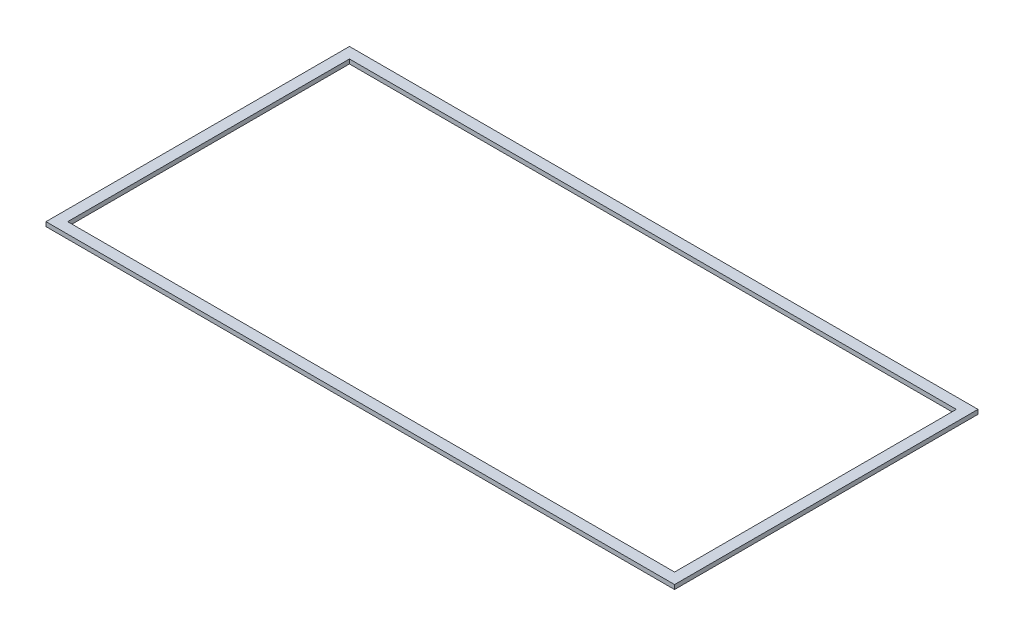
SolidWorks part; units mm, degrees
material "Rubber"
ref_plane "Front Plane" through (0, 0, 0) normal (0, 0, 1) x (1, 0, 0)
ref_plane "Top Plane" through (0, 0, 0) normal (0, 1, 0) x (1, 0, 0)
ref_plane "Right Plane" through (0, 0, 0) normal (1, 0, 0) x (0, 0, -1)
sketch "Sketch1" plane through (0, 0, 0) normal (0, 1, 0) x (1, 0, 0)
  line L1 (-140, -65) -> (140, -65)
  line L2 (-140, -65) -> (-140, 65)
  line L3 (-140, 65) -> (140, 65)
  line L4 (140, -65) -> (140, 65)
  line L5 (-140, -65) -> (140, 65) construction
  line L6 (-140, 65) -> (140, -65) construction
  line L7 (-145, -70) -> (145, -70)
  line L8 (-145, -70) -> (-145, 70)
  line L9 (-145, 70) -> (145, 70)
  line L10 (145, -70) -> (145, 70)
  line L11 (-145, -70) -> (145, 70) construction
  line L12 (-145, 70) -> (145, -70) construction
  point P0 (0, 0)
  point P6 (0, 0)
  dimension "D1" = 130
  dimension "D2" = 280
  dimension "D3" = 290
  dimension "D4" = 140
extrude "Boss-Extrude1" add sketch "Sketch1" along normal blind 2
